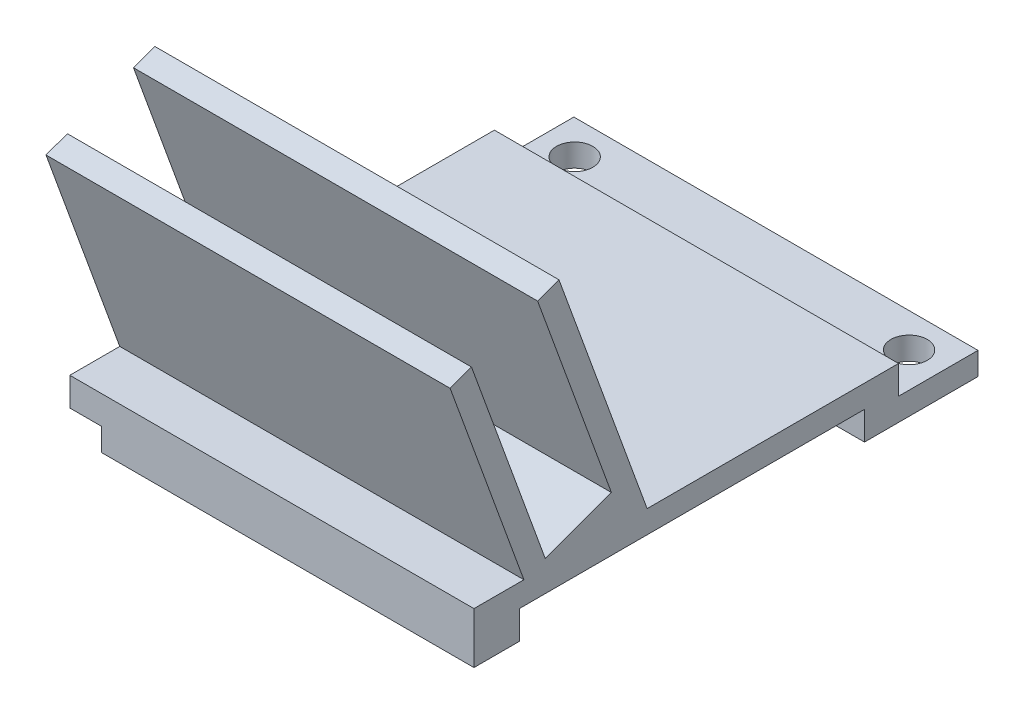
SolidWorks part; units mm, degrees
ref_plane "Front Plane" through (0, 0, 0) normal (0, 0, 1) x (1, 0, 0)
ref_plane "Top Plane" through (0, 0, 0) normal (0, 1, 0) x (1, 0, 0)
ref_plane "Right Plane" through (0, 0, 0) normal (1, 0, 0) x (0, 0, -1)
sketch "Sketch1" plane through (0, 0, 0) normal (0, 1, 0) x (1, 0, 0)
  line L1 (-17.8, 3) -> (17.8, 3)
  line L2 (-17.8, 3) -> (-17.8, -3)
  line L4 (17.8, 3) -> (17.8, -3)
  line L8 (-17.8, -3) -> (-17.8, -7)
  line L9 (-17.8, -7) -> (17.8, -7)
  line L10 (17.8, -3) -> (17.8, -7)
  circle A0 centre (-14.73, 0) radius 1.4
  circle A1 centre (14.73, 0) radius 1.4
  point P4 (0, 0)
  point P7 (0, 0)
extrude "Boss-Extrude1" add sketch "Sketch1" along normal blind 2
sketch "Sketch2" plane through (0, 2, 0) normal (0, 1, 0) x (1, 0, 0)
  line L0 (17.8, -7) -> (17.8, 3) construction
  line L1 (-17.8, -7) -> (17.8, -7)
  line L2 (-17.8, -7) -> (-17.8, -3)
  line L3 (-17.8, -3) -> (17.8, -3)
  line L4 (17.8, -7) -> (17.8, -3)
extrude "Boss-Extrude2" add sketch "Sketch2" along normal blind 2.5
sketch "Sketch3" plane through (0, 0, 7) normal (0, 0, 1) x (1, 0, 0)
  line L0 (17.8, 4.5) -> (17.8, 0) construction
  line L1 (-17.8, 4.5) -> (17.8, 4.5)
  line L2 (-17.8, 4.5) -> (-17.8, 2.5)
  line L3 (-17.8, 2.5) -> (17.8, 2.5)
  line L4 (17.8, 4.5) -> (17.8, 2.5)
extrude "Boss-Extrude3" add sketch "Sketch3" along normal blind 30
sketch "Sketch4" plane through (0, 2.5, 0) normal (0, -1, 0) x (1, 0, 0)
  line L1 (-17.8, 37) -> (-14.8, 37)
  line L2 (-17.8, 37) -> (-17.8, 27)
  line L3 (-17.8, 27) -> (-14.8, 27)
  line L4 (-14.8, 37) -> (-14.8, 27)
  line L5 (17.8, 37) -> (14.8, 37)
  line L6 (17.8, 37) -> (17.8, 27)
  line L7 (17.8, 27) -> (14.8, 27)
  line L8 (14.8, 37) -> (14.8, 27)
extrude "Boss-Extrude4" add sketch "Sketch4" along normal up to surface (2.5 mm away) up to face at (0, 0, 2)
sketch "Sketch5" plane through (0, 4.5, 0) normal (0, 1, 0) x (1, 0, 0)
  line L0 (17.8, -37) -> (17.8, -3) construction
  line L1 (-17.8, -37) -> (17.8, -37)
  line L2 (-17.8, -37) -> (-17.8, -35)
  line L3 (-17.8, -35) -> (17.8, -35)
  line L4 (17.8, -37) -> (17.8, -35)
  line L6 (-17.8, -3) -> (-17.8, -37) construction
  line L8 (-17.8, -28.75) -> (17.8, -28.75)
  line L9 (-17.8, -28.75) -> (-17.8, -26.75)
  line L10 (-17.8, -26.75) -> (17.8, -26.75)
  line L11 (17.8, -28.75) -> (17.8, -26.75)
extrude "Boss-Extrude5" add sketch "Sketch5" along normal blind 20
sketch "Sketch6" plane through (0, 2.5, 0) normal (0, -1, 0) x (1, 0, 0)
  line L0 (14.8, 27) -> (14.8, 37) construction
  line L1 (-14.8, 37) -> (14.8, 37)
  line L2 (-14.8, 37) -> (-14.8, 33)
  line L3 (-14.8, 33) -> (14.8, 33)
  line L4 (14.8, 37) -> (14.8, 33)
extrude "Boss-Extrude6" add sketch "Sketch6" along normal up to surface (2.5 mm away) up to face at (16.3, 0, 32)
sketch "Sketch7" plane through (0, 0, 37) normal (0, 0, 1) x (1, 0, 0)
  line L4 (-17.8, 24.5) -> (-17.8, 0)
  line L5 (-17.8, 0) -> (17.8, 0)
  line L6 (17.8, 0) -> (17.8, 24.5)
  line L7 (17.8, 24.5) -> (-17.8, 24.5)
  line L8 (-17.8, 24.5) -> (-17.8, 0)
  line L9 (-17.8, 0) -> (17.8, 0)
  line L10 (17.8, 0) -> (17.8, 24.5)
  line L11 (17.8, 24.5) -> (-17.8, 24.5)
  dimension "D1" = 0
extrude "Boss-Extrude7" add sketch "Sketch7" along normal blind 4.4
sketch "Sketch8" plane through (0, 0, 33) normal (0, 0, -1) x (-1, 0, 0)
  line L4 (-14.8, 2.5) -> (-14.8, 0)
  line L5 (-14.8, 0) -> (14.8, 0)
  line L6 (14.8, 0) -> (14.8, 2.5)
  line L7 (14.8, 2.5) -> (-14.8, 2.5)
  line L8 (-14.8, 2.5) -> (-14.8, 0)
  line L9 (-14.8, 0) -> (14.8, 0)
  line L10 (14.8, 0) -> (14.8, 2.5)
  line L11 (14.8, 2.5) -> (-14.8, 2.5)
  dimension "D1" = 0
extrude "Cut-Extrude1" cut sketch "Sketch8" against normal blind 4.4
sketch "Sketch9" plane through (0, 0, 27) normal (0, 0, -1) x (-1, 0, 0)
  line L4 (-17.8, 2.5) -> (-17.8, 0)
  line L5 (-17.8, 0) -> (-14.8, 0)
  line L6 (-14.8, 0) -> (-14.8, 2.5)
  line L7 (-14.8, 2.5) -> (-17.8, 2.5)
  line L8 (-17.8, 2.5) -> (-17.8, 0)
  line L9 (-17.8, 0) -> (-14.8, 0)
  line L10 (-14.8, 0) -> (-14.8, 2.5)
  line L11 (-14.8, 2.5) -> (-17.8, 2.5)
  line L12 (14.8, 2.5) -> (14.8, 0)
  line L13 (14.8, 0) -> (17.8, 0)
  line L14 (17.8, 0) -> (17.8, 2.5)
  line L15 (17.8, 2.5) -> (14.8, 2.5)
  line L16 (14.8, 2.5) -> (14.8, 0)
  line L17 (14.8, 0) -> (17.8, 0)
  line L18 (17.8, 0) -> (17.8, 2.5)
  line L19 (17.8, 2.5) -> (14.8, 2.5)
  dimension "D1" = 0
  dimension "D2" = 0
extrude "Cut-Extrude2" cut sketch "Sketch9" against normal blind 4.4
sketch "Sketch10" plane through (0, 0, 41.4) normal (0, 0, 1) x (1, 0, 0)
  line L4 (-17.8, 4.5) -> (17.8, 4.5)
  line L5 (17.8, 4.5) -> (17.8, 24.5)
  line L6 (17.8, 24.5) -> (-17.8, 24.5)
  line L7 (-17.8, 24.5) -> (-17.8, 4.5)
  line L8 (-17.8, 4.5) -> (17.8, 4.5)
  line L9 (17.8, 4.5) -> (17.8, 24.5)
  line L10 (17.8, 24.5) -> (-17.8, 24.5)
  line L11 (-17.8, 24.5) -> (-17.8, 4.5)
  dimension "D1" = 0
extrude "Cut-Extrude3" cut sketch "Sketch10" against normal blind 4.4
sketch "Sketch11" plane through (0, 0, 0) normal (0, -1, 0) x (1, 0, 0)
  circle A0 centre (-14.73, 0) radius 1.6
  circle A1 centre (14.73, 0) radius 1.6
extrude "Cut-Extrude4" cut sketch "Sketch11" against normal blind 10
sketch "Sketch12" plane through (0, 0, 3) normal (0, 0, -1) x (-1, 0, 0)
  line L4 (-17.8, 2) -> (17.8, 2)
  line L5 (17.8, 2) -> (17.8, 4.5)
  line L6 (17.8, 4.5) -> (-17.8, 4.5)
  line L7 (-17.8, 4.5) -> (-17.8, 2)
  line L8 (-17.8, 2) -> (17.8, 2)
  line L9 (17.8, 2) -> (17.8, 4.5)
  line L10 (17.8, 4.5) -> (-17.8, 4.5)
  line L11 (-17.8, 4.5) -> (-17.8, 2)
  dimension "D1" = 0
extrude "Cut-Extrude5" cut sketch "Sketch12" against normal blind 1
sketch "Sketch13" plane through (0, 24.5, 0) normal (0, 1, 0) x (1, 0, 0)
  line L1 (-17.8, -26.75) -> (17.8, -26.75)
  line L2 (-17.8, -26.75) -> (-17.8, -37)
  line L3 (-17.8, -37) -> (17.8, -37)
  line L4 (17.8, -26.75) -> (17.8, -37)
extrude "Cut-Extrude6" cut sketch "Sketch13" against normal blind 1
sketch "Sketch14" plane through (0, 0, 28.75) normal (0, 0, 1) x (1, 0, 0)
  line L4 (17.8, 23.5) -> (-17.8, 23.5)
  line L5 (-17.8, 23.5) -> (-17.8, 4.5)
  line L6 (-17.8, 4.5) -> (17.8, 4.5)
  line L7 (17.8, 4.5) -> (17.8, 23.5)
  line L8 (17.8, 23.5) -> (-17.8, 23.5)
  line L9 (-17.8, 23.5) -> (-17.8, 4.5)
  line L10 (-17.8, 4.5) -> (17.8, 4.5)
  line L11 (17.8, 4.5) -> (17.8, 23.5)
  dimension "D1" = 0
extrude "Boss-Extrude8" add sketch "Sketch14" along normal blind 0.05
sketch "Sketch15" plane through (-17.8, 0, 0) normal (-1, 0, 0) x (0, 0, 1)
  line L0 (35.1206, 5.184) -> (41.619, 23.0382)
  line L2 (37, 4.5) -> (43.4984, 22.3542)
  line L3 (37, 4.5) -> (34.8716, 4.5)
  line L6 (41.619, 23.0382) -> (43.4984, 22.3542)
  line L7 (29.2945, 7.3046) -> (35.1206, 5.184)
  line L8 (29.2945, 7.3046) -> (35.7929, 25.1587)
  line L9 (35.7929, 25.1587) -> (33.9135, 25.8428)
  line L10 (33.9135, 25.8428) -> (27.4151, 7.9886)
  line L12 (27.4151, 7.9886) -> (26.1454, 4.5)
  line L13 (4, 4.5) -> (26.75, 4.5) construction
  line L14 (26.1454, 4.5) -> (34.8716, 4.5)
  dimension "D1" = 2
extrude "Boss-Extrude9" add sketch "Sketch15" against normal up to surface (35.6 mm away) up to face at (17.8, 7.2222, 23.15)
sketch "Sketch16" plane through (0, -7.8766, 21.6407) normal (0, 0.342, -0.9397) x (-1, 0, 0)
  line L4 (-17.8, 31.2318) -> (-17.8, 14.9386)
  line L5 (-17.8, 14.9386) -> (17.8, 14.9386)
  line L6 (17.8, 14.9386) -> (17.8, 31.2318)
  line L7 (17.8, 31.2318) -> (-17.8, 31.2318)
  line L8 (-17.8, 31.2318) -> (-17.8, 14.9386)
  line L9 (-17.8, 14.9386) -> (17.8, 14.9386)
  line L10 (17.8, 14.9386) -> (17.8, 31.2318)
  line L11 (17.8, 31.2318) -> (-17.8, 31.2318)
  dimension "D1" = 0
extrude "Cut-Extrude7" cut sketch "Sketch16" along normal blind 29
sketch "Sketch17" plane through (0, -8.5606, 23.5201) normal (0, -0.342, 0.9397) x (1, 0, 0)
  line L0 (-17.8, 33.5651) -> (-17.8, 35.8834)
  line L1 (-17.8, 35.8834) -> (17.8, 35.8834)
  line L2 (17.8, 35.8834) -> (17.8, 33.5651)
  line L4 (17.8, 33.5651) -> (-17.8, 33.5651)
  line L5 (-17.8, 33.5651) -> (-17.8, 16.8834)
  line L6 (-17.8, 16.8834) -> (17.8, 16.8834)
  line L7 (17.8, 16.8834) -> (17.8, 33.5651)
  line L9 (-17.8, 33.5651) -> (-17.8, 16.8834)
  line L10 (-17.8, 16.8834) -> (17.8, 16.8834)
  line L11 (17.8, 16.8834) -> (17.8, 33.5651)
  dimension "D1" = 0
extrude "Cut-Extrude8" cut sketch "Sketch17" along normal up to surface (6.2 mm away) up to face at (0, 16.6929, 39.3095)
sketch "Sketch19" plane through (14.8, 0, 0) normal (-1, 0, 0) x (0, 0, 1)
  line L4 (31.4, 2.5) -> (31.4, 0)
  line L5 (31.4, 0) -> (37.4, 0)
  line L6 (37.4, 0) -> (37.4, 2.5)
  line L7 (37.4, 2.5) -> (31.4, 2.5)
  line L8 (31.4, 2.5) -> (31.4, 0)
  line L9 (31.4, 0) -> (37.4, 0)
  line L10 (37.4, 0) -> (37.4, 2.5)
  line L11 (37.4, 2.5) -> (31.4, 2.5)
  dimension "D1" = 0
extrude "Cut-Extrude9" cut sketch "Sketch19" against normal blind 29
sketch "Sketch20" plane through (0, 0, 0) normal (0, -1, 0) x (1, 0, 0)
  line L1 (-17.8, 41.4) -> (-15, 41.4)
  line L2 (-17.8, 41.4) -> (-17.8, 38.6)
  line L3 (-17.8, 38.6) -> (-15, 38.6)
  line L4 (-15, 41.4) -> (-15, 38.6)
extrude "Cut-Extrude10" cut sketch "Sketch20" against normal blind 2
